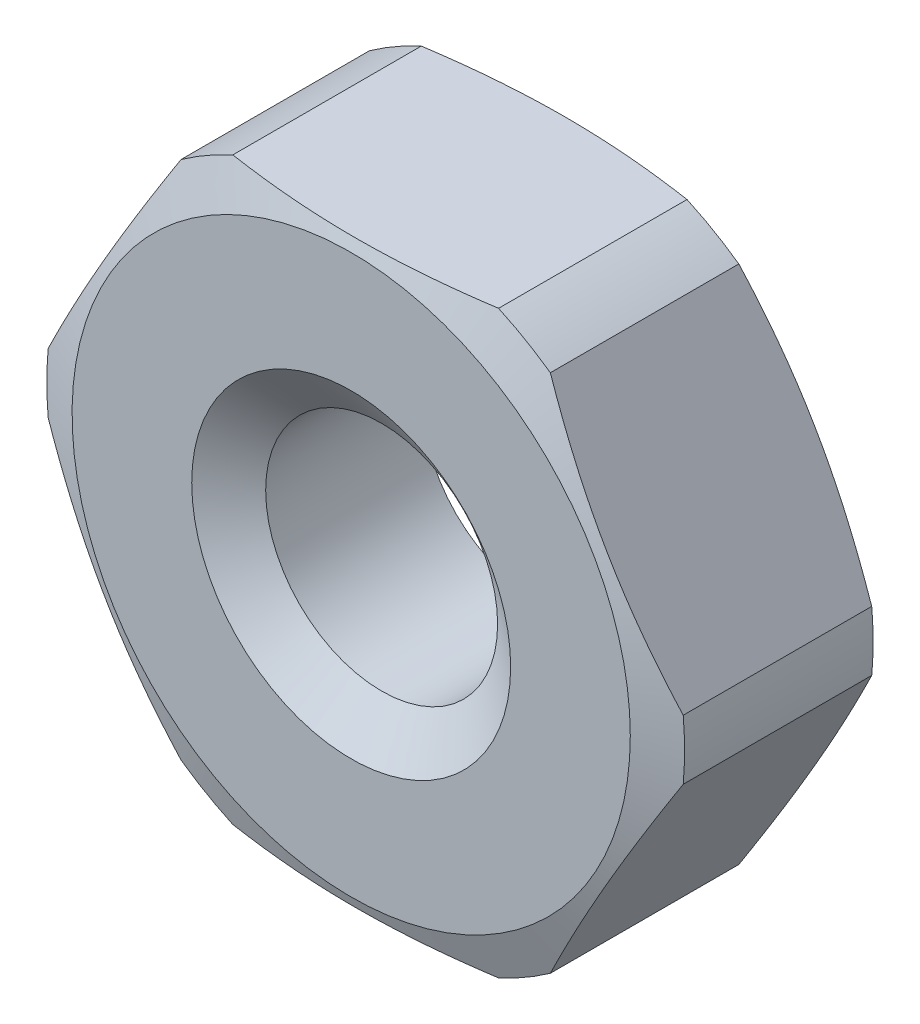
SolidWorks part; units mm, degrees
ref_plane "Спереди" through (0, 0, 0) normal (0, 0, 1) x (1, 0, 0)
ref_plane "Сверху" through (0, 0, 0) normal (0, 1, 0) x (1, 0, 0)
ref_plane "Справа" through (0, 0, 0) normal (1, 0, 0) x (0, 0, -1)
sketch "Эскиз1" plane through (0, 0, 0) normal (0, 0, 1) x (1, 0, 0)
  line L1 (2.3094, 0) -> (1.1547, 2)
  line L2 (1.1547, 2) -> (-1.1547, 2)
  line L3 (-1.1547, 2) -> (-2.3094, 0)
  line L4 (-2.3094, 0) -> (-1.1547, -2)
  line L5 (-1.1547, -2) -> (1.1547, -2)
  line L6 (1.1547, -2) -> (2.3094, 0)
  circle A0 centre (0, 0) radius 2 construction
  circle A1 centre (0, 0) radius 0.8
  dimension "D1" = 4
  dimension "D2" = 1.6
extrude "Бобышка-Вытянуть1" add sketch "Эскиз1" along normal blind 1.5
cosmetic thread "Отверстие резьбы1" parameters "D2"=2
sketch "Эскиз2" plane through (0, 0, 0) normal (0, 1, 0) x (1, 0, 0)
  line L0 (0, 0) -> (0, -1.5) construction
  line L1 (1.1547, -1.5) -> (-1.1547, -1.5) construction
  line L2 (1.9253, 0) -> (2.2, -0.1)
  line L3 (2.3094, 0) -> (1.1547, 0) construction
  line L4 (2.2, -0.1) -> (2.2, -1.4)
  line L5 (2.2, -1.4) -> (1.9253, -1.5)
  line L6 (2.3094, -1.5) -> (1.1547, -1.5) construction
  line L7 (1.9253, 0) -> (1.9253, 0.2958)
  line L8 (1.9253, 0.2958) -> (2.7725, 0.2958)
  line L9 (2.7725, 0.2958) -> (2.7725, -1.7767)
  line L10 (2.7725, -1.7767) -> (1.9253, -1.7767)
  line L11 (1.9253, -1.7767) -> (1.9253, -1.5)
  dimension "D1" = 4.4
  dimension "D3" = 0.1
  dimension "D4" = 20
revolve "Вырез-Повернуть1" cut sketch "Эскиз2" angle 360 about L0
hole_wizard "Отверстие обработанное метчиком M2x0.41" positions "Эскиз4" profile "Эскиз3" tap size "M2x0.4" standard "Ansi (метрические)" end condition through all
sketch "Эскиз4" plane through (0, 0, 0) normal (0, 0, -1) x (-1, 0, 0)
  point P1 (0, 0)
sketch "Эскиз3" plane through (0, 0, 0) normal (1, 0, 0) x (0, 1, 0)
  line L0 (0, 0) -> (0, 1.5)
  line L1 (0, 1.5) -> (1.1, 1.5)
  line L2 (0.8, 1.2899) -> (0.8, 0.2101)
  line L3 (0.8, 0.2101) -> (1.1, 0)
  line L5 (1.1, 0) -> (0, 0)
  line L6 (-0.8, 0.2101) -> (-1.1, 0) construction
  line L7 (1.1, 1.5) -> (0.8, 1.2899)
  line L8 (-1.1, 1.5) -> (-0.8, 1.2899) construction
  line L11 (0, -6.35) -> (0, 107.95) construction
  dimension "Диаметр проходного сверла" = 1.6
  dimension "Глубина проходного сверла" = 1.5
  dimension "Диаметр передней зенковки" = 2.2
  dimension "Угол передней зенковки" = 110
  dimension "Диаметр задней зенковки" = 2.2
  dimension "Угол задней зенковки" = 110
